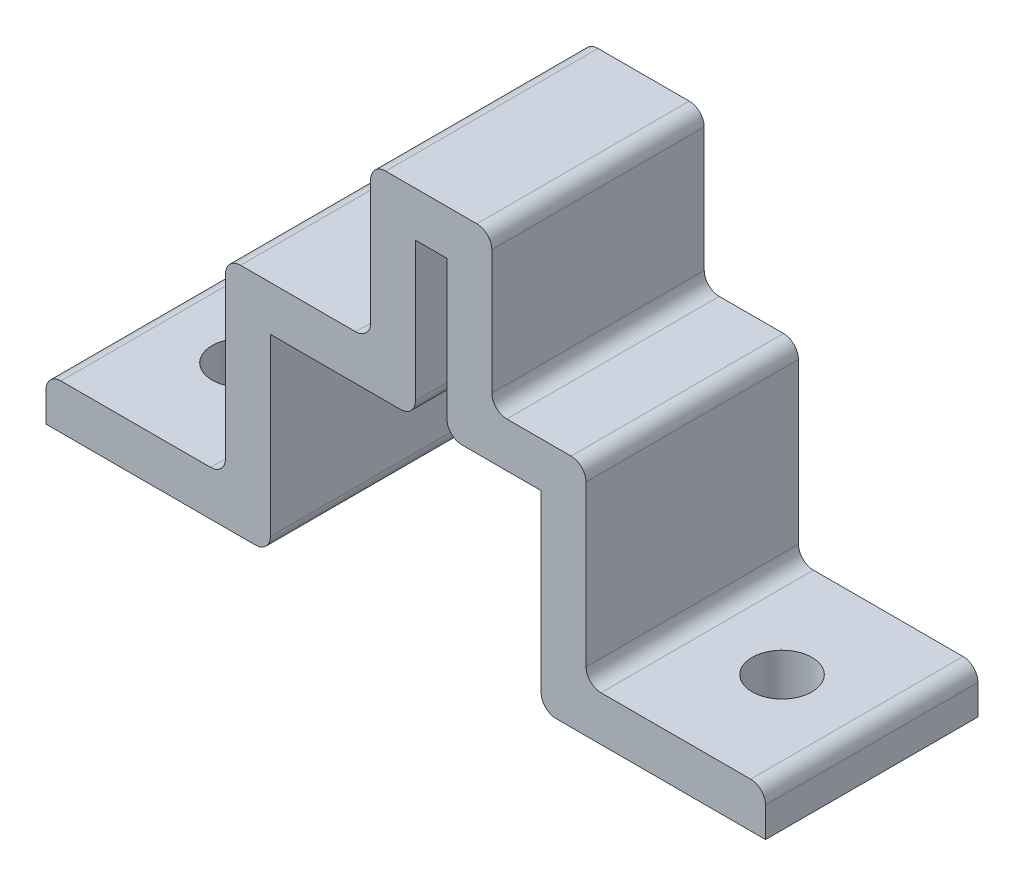
SolidWorks part; units mm, degrees
ref_plane "Front" through (0, 0, 0) normal (0, 0, 1) x (1, 0, 0)
ref_plane "Top" through (0, 0, 0) normal (0, 1, 0) x (1, 0, 0)
ref_plane "Right" through (0, 0, 0) normal (1, 0, 0) x (0, 0, -1)
sketch "Sketch1" plane through (0, 0, 0) normal (0, 0, 1) x (1, 0, 0)
  line L0 (0, 0) -> (12, 0)
  line L1 (12, 14.7) -> (12, 4)
  line L2 (11, 3) -> (1, 3)
  line L3 (12, 0) -> (14, 0)
  line L4 (15, 1) -> (15, 12.7)
  line L5 (15, 12.7) -> (23.7, 12.7)
  line L6 (24.7, 13.7) -> (24.7, 23)
  line L7 (24.7, 23) -> (26.8, 23)
  line L8 (26.8, 23) -> (26.8, 13.7)
  line L9 (27.8, 12.7) -> (33.1, 12.7)
  line L10 (33.1, 12.7) -> (33.1, 1)
  line L11 (34.1, 0) -> (48.1, 0)
  line L12 (0, 2) -> (0, 0)
  line L13 (13, 15.7) -> (20.7, 15.7)
  line L14 (21.7, 16.7) -> (21.7, 25)
  line L15 (22.7, 26) -> (28.8, 26)
  line L16 (29.8, 25) -> (29.8, 16.7)
  line L17 (30.8, 15.7) -> (35.1, 15.7)
  line L18 (36.1, 14.7) -> (36.1, 4)
  line L19 (48.1, 0) -> (48.1, 2)
  line L20 (0, 3) -> (12, 3) construction
  line L21 (12, 3) -> (12, 15.7) construction
  line L22 (12, 3) -> (12, 3) construction
  line L23 (36.1, 15.7) -> (36.1, 3) construction
  line L24 (36.1, 3) -> (45.1, 3) construction
  line L25 (29.8, 15.7) -> (36.1, 15.7) construction
  line L26 (29.8, 26) -> (29.8, 15.7) construction
  line L27 (21.7, 26) -> (29.8, 26) construction
  line L28 (21.7, 15.7) -> (21.7, 26) construction
  line L29 (12, 15.7) -> (21.7, 15.7) construction
  line L30 (47.1, 3) -> (37.1, 3)
  line L31 (33.1, 12.7) -> (33.1, 0) construction
  line L32 (33.1, 0) -> (45.1, 0) construction
  line L33 (12, 0) -> (15, 0) construction
  line L34 (15, 0) -> (15, 12.7) construction
  line L35 (26.8, 23) -> (26.8, 12.7) construction
  line L36 (26.8, 12.7) -> (33.1, 12.7) construction
  line L37 (15, 12.7) -> (24.7, 12.7) construction
  line L38 (24.7, 12.7) -> (24.7, 23) construction
  arc A0 (36.1, 4) -> (37.1, 3) centre (37.1, 4) ccw
  arc A1 (35.1, 15.7) -> (36.1, 14.7) centre (35.1, 14.7) cw
  arc A2 (29.8, 16.7) -> (30.8, 15.7) centre (30.8, 16.7) ccw
  arc A3 (28.8, 26) -> (29.8, 25) centre (28.8, 25) cw
  arc A4 (21.7, 25) -> (22.7, 26) centre (22.7, 25) cw
  arc A5 (20.7, 15.7) -> (21.7, 16.7) centre (20.7, 16.7) ccw
  arc A6 (12, 14.7) -> (13, 15.7) centre (13, 14.7) cw
  arc A7 (12, 4) -> (11, 3) centre (11, 4) cw
  arc A8 (1, 3) -> (0, 2) centre (1, 2) ccw
  arc A9 (48.1, 2) -> (47.1, 3) centre (47.1, 2) ccw
  arc A10 (33.1, 1) -> (34.1, 0) centre (34.1, 1) ccw
  arc A11 (14, 0) -> (15, 1) centre (14, 1) ccw
  arc A12 (26.8, 13.7) -> (27.8, 12.7) centre (27.8, 13.7) ccw
  arc A13 (23.7, 12.7) -> (24.7, 13.7) centre (23.7, 13.7) ccw
  dimension "D2" = 1
  dimension "D3" = 1
  dimension "D4" = 1
  dimension "D1" = 3
extrude "Boss-Extrude1" add sketch "Sketch1" against normal blind 14.2
sketch "Sketch2" plane through (0, 0, 0) normal (0, 1, 0) x (1, 0, 0)
  line L0 (1, 0) -> (6, 0) construction
  line L1 (11, 0) -> (1, 0) construction
  line L2 (6, 0) -> (6, 7.1) construction
  line L3 (47.1, 0) -> (42.1, 0) construction
  line L4 (47.1, 0) -> (37.1, 0) construction
  line L5 (42.1, 0) -> (42.1, 7.1) construction
  circle A0 centre (42.1, 7.1) radius 2
  circle A1 centre (6, 7.1) radius 2
extrude "Cut-Extrude1" cut sketch "Sketch2" along normal up to surface (3 mm away) up to face at (42.1, 3, -7.1)
